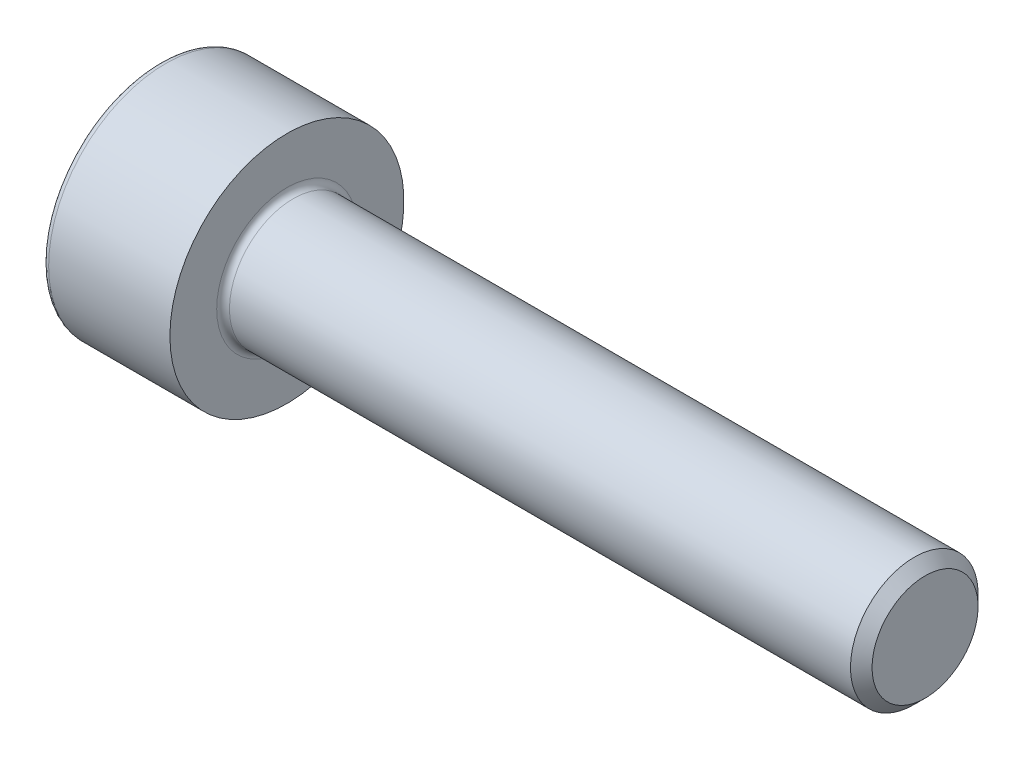
SolidWorks part; units mm, degrees
ref_plane "Front" through (0, 0, 0) normal (0, 0, 1) x (1, 0, 0)
ref_plane "Top" through (0, 0, 0) normal (0, 1, 0) x (1, 0, 0)
ref_plane "Right" through (0, 0, 0) normal (1, 0, 0) x (0, 0, -1)
sketch "Sketch1" plane through (0, 0, 0) normal (0, 0, 1) x (1, 0, 0)
  line L0 (14.7465, 1.5) -> (0.15, 1.5)
  line L1 (-3, 2.6) -> (-3, 0)
  line L2 (0, 2.75) -> (-2.85, 2.75)
  line L3 (0, 1.65) -> (0, 2.75)
  line L4 (15, 1.2465) -> (15, 0)
  line L5 (15, 1.2465) -> (14.7465, 1.5)
  line L6 (-3, 0) -> (0, 0) construction
  line L7 (-3, 0) -> (15, 0)
  arc A0 (-2.85, 2.75) -> (-3, 2.6) centre (-2.85, 2.6) ccw
  arc A1 (0, 1.65) -> (0.15, 1.5) centre (0.15, 1.65) ccw
  point P12 (0, 2.2)
  dimension "D5" = 0.15
  dimension "D1" = 3
  dimension "D2" = 5.5
  dimension "D3" = 135
  dimension "D4" = 0.3585
  dimension "D6" = 15
  dimension "D7" = 3
revolve "Revolve1" add sketch "Sketch1" angle 360 about L7
sketch "Sketch2" plane through (-3, 0, 0) normal (-1, 0, 0) x (0, 0, 1)
  line L7 (1.28, 0.739) -> (0, 1.478)
  line L8 (0, 1.478) -> (-1.28, 0.739)
  line L9 (-1.28, 0.739) -> (-1.28, -0.739)
  line L10 (-1.28, -0.739) -> (0, -1.478)
  line L11 (0, -1.478) -> (1.28, -0.739)
  line L12 (1.28, -0.739) -> (1.28, 0.739)
  circle A0 centre (0, 0) radius 1.28 construction
  dimension "D1" = 2.56
extrude "Cut-Extrude1" cut sketch "Sketch2" against normal blind 1.3
